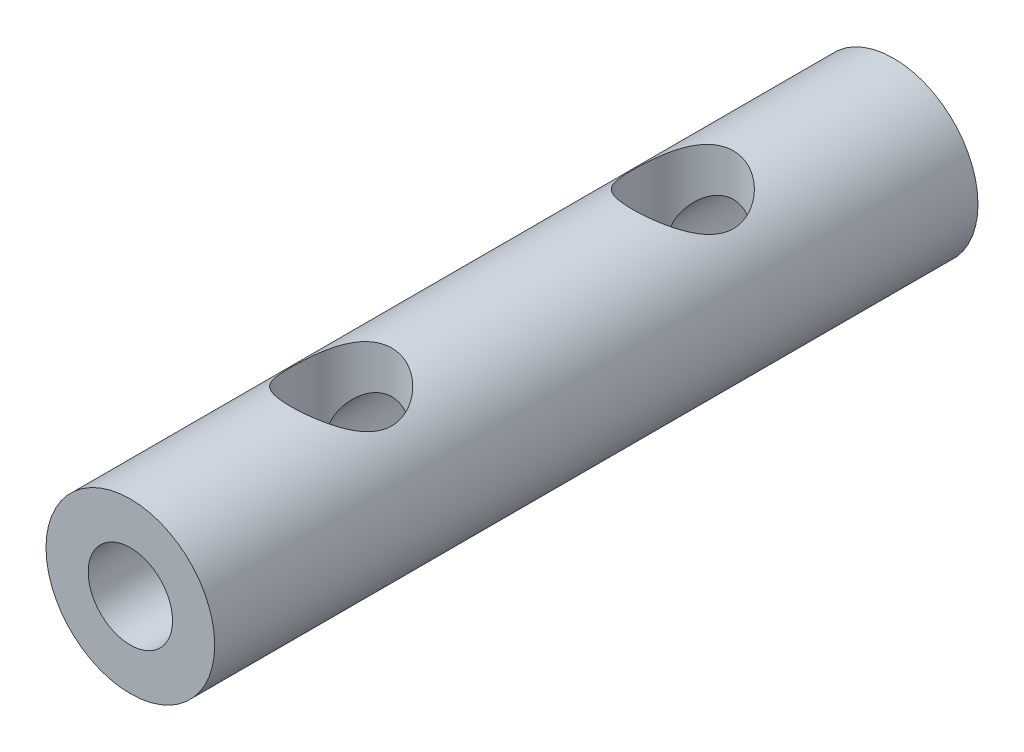
SolidWorks part; units mm, degrees
ref_plane "Front Plane" through (0, 0, 0) normal (0, 0, 1) x (1, 0, 0)
ref_plane "Top Plane" through (0, 0, 0) normal (0, 1, 0) x (1, 0, 0)
ref_plane "Right Plane" through (0, 0, 0) normal (1, 0, 0) x (0, 0, -1)
sketch "Sketch1" plane through (0, 0, 0) normal (0, 0, 1) x (1, 0, 0)
  circle A0 centre (0, 0) radius 10
  dimension "D1" = 20
extrude "Boss-Extrude1" add sketch "Sketch1" along normal blind 90.5
sketch "Sketch2" plane through (0, 0, 90.5) normal (0, 0, 1) x (1, 0, 0)
  circle A0 centre (0, 0) radius 5
  dimension "D1" = 10
extrude "Cut-Extrude1" cut sketch "Sketch2" against normal through all
ref_plane "Plane1" through (0, 10, 0) normal (0, 1, 0) x (1, 0, 0)
sketch "Sketch3" plane through (0, 10, 0) normal (0, 1, 0) x (1, 0, 0)
  line L0 (0, 0) -> (0, -98.7845) construction
  line L1 (10, 0) -> (-10, 0) construction
  line L2 (-10, -90.5) -> (10, -90.5) construction
  circle A0 centre (0, -25) radius 6
  circle A1 centre (0, -65.5) radius 6
  dimension "D2" = 25
  dimension "D1" = 25
  dimension "D3" = 12
  dimension "D4" = 12
extrude "Cut-Extrude2" cut sketch "Sketch3" against normal through all
